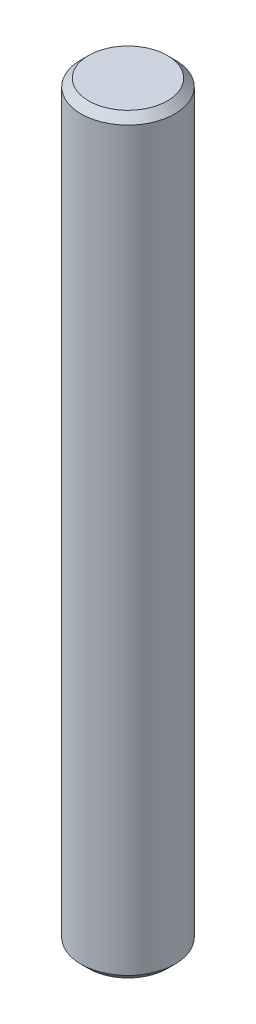
SolidWorks part; units mm, degrees
ref_plane "Front Plane" through (0, 0, 0) normal (0, 0, 1) x (1, 0, 0)
ref_plane "Top Plane" through (0, 0, 0) normal (0, 1, 0) x (1, 0, 0)
ref_plane "Right Plane" through (0, 0, 0) normal (1, 0, 0) x (0, 0, -1)
ref_plane "Plane1" through (0, 0, 0) normal (0, 0, -1) x (-1, 0, 0)
sketch "Sketch1" plane through (0, 0, 0) normal (0, 0, -1) x (-1, 0, 0)
  line L0 (-2.6632, 0) -> (0, 0)
  line L1 (0, 0) -> (0, 50.8)
  line L2 (0, 50.8) -> (-2.6632, 50.8)
  line L3 (-2.6632, 50.8) -> (-3.1712, 50.292)
  line L4 (-3.1712, 50.292) -> (-3.1712, 0.508)
  line L5 (-3.1712, 0.508) -> (-2.6632, 0)
  line L6 (0, 0) -> (0, 50.8) construction
revolve "Revolve1" add sketch "Sketch1" angle 360 about L6
